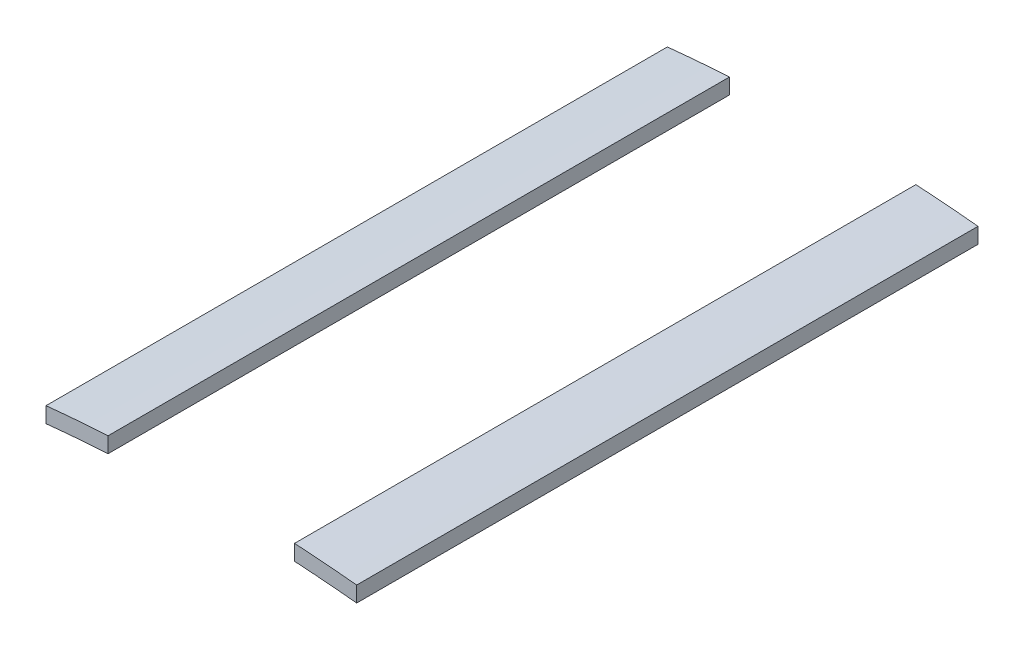
SolidWorks part; units mm, degrees
ref_plane "Front Plane" through (0, 0, 0) normal (0, 0, 1) x (1, 0, 0)
ref_plane "Top Plane" through (0, 0, 0) normal (0, 1, 0) x (1, 0, 0)
ref_plane "Right Plane" through (0, 0, 0) normal (1, 0, 0) x (0, 0, -1)
sketch "Sketch3" plane through (0, 0, 0) normal (1, 0, 0) x (0, 0, -1)
  line L0 (11.4481, 5.2748) -> (-16.7252, 5.2748) construction
  line L1 (-13.6293, 0.2748) -> (-13.6293, 2.2748)
  line L2 (6.3707, 10.2748) -> (-13.6293, 10.2748)
  line L3 (6.3707, 10.2748) -> (6.3707, 8.2748)
  line L4 (6.3707, 8.2748) -> (-13.6293, 8.2748)
  line L5 (-13.6293, 10.2748) -> (-13.6293, 8.2748)
  line L6 (6.3707, 2.2748) -> (-13.6293, 2.2748)
  line L7 (6.3707, 0.2748) -> (6.3707, 2.2748)
  line L8 (6.3707, 0.2748) -> (-13.6293, 0.2748)
  dimension "D1" = 20
  dimension "D2" = 2
  dimension "D3" = 3
extrude "Boss-Extrude3" [suppressed] add sketch "Sketch3" along normal blind 0.5
sketch "Sketch4" plane through (0, 0, 0) normal (0, 0, 1) x (1, 0, 0)
  line L0 (5, 49.2468) -> (5, 48.7442)
  line L1 (3, 49.409) -> (3, 48.9081)
  line L2 (-3, 49.409) -> (-3, 48.9081)
  line L3 (-5, 49.2468) -> (-5, 48.7442)
  line L4 (0, -55) -> (0, 55) construction
  arc A0 (5, 49.2468) -> (3, 49.409) centre (0, 0) ccw
  arc A1 (5, 48.7442) -> (3, 48.9081) centre (0, 0) ccw
  arc A2 (-3, 49.409) -> (-5, 49.2468) centre (0, 0) ccw
  arc A3 (-3, 48.9081) -> (-5, 48.7442) centre (0, 0) ccw
  dimension "D1" = 98
  dimension "D2" = 99
  dimension "D3" = 2
  dimension "D4" = 3
  dimension "D5" = 6
  dimension "D6" = 2
extrude "Boss-Extrude4" add sketch "Sketch4" along normal blind 20
